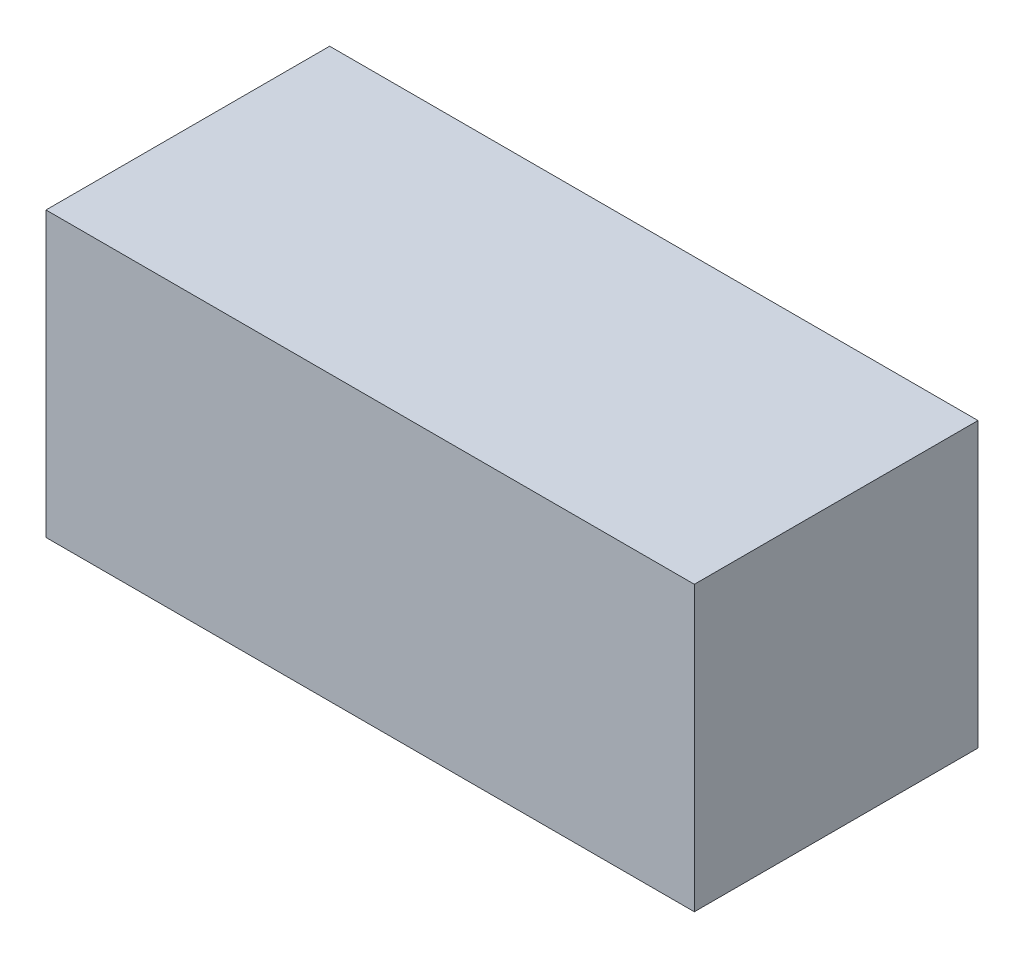
SolidWorks part; units mm, degrees
ref_plane "정면" through (0, 0, 0) normal (0, 0, 1) x (1, 0, 0)
ref_plane "윗면" through (0, 0, 0) normal (0, 1, 0) x (1, 0, 0)
ref_plane "우측면" through (0, 0, 0) normal (1, 0, 0) x (0, 0, -1)
sketch "스케치1" plane through (0, 0, 0) normal (0, 0, 1) x (1, 0, 0)
  line L1 (0, 0) -> (160, 0)
  line L2 (0, 0) -> (0, -70)
  line L3 (0, -70) -> (160, -70)
  line L4 (160, 0) -> (160, -70)
  dimension "D1" = 160
  dimension "D2" = 70
extrude "보스-돌출1" add sketch "스케치1" along normal blind 70
sketch "스케치2" plane through (0, 0, 0) normal (0, 0, -1) x (-1, 0, 0)
  text T0 "CHILLER MODULE\r\n\r\n" font "Century Gothic" height in points 48
extrude "보스-돌출2" add sketch "스케치2" along normal blind 1
